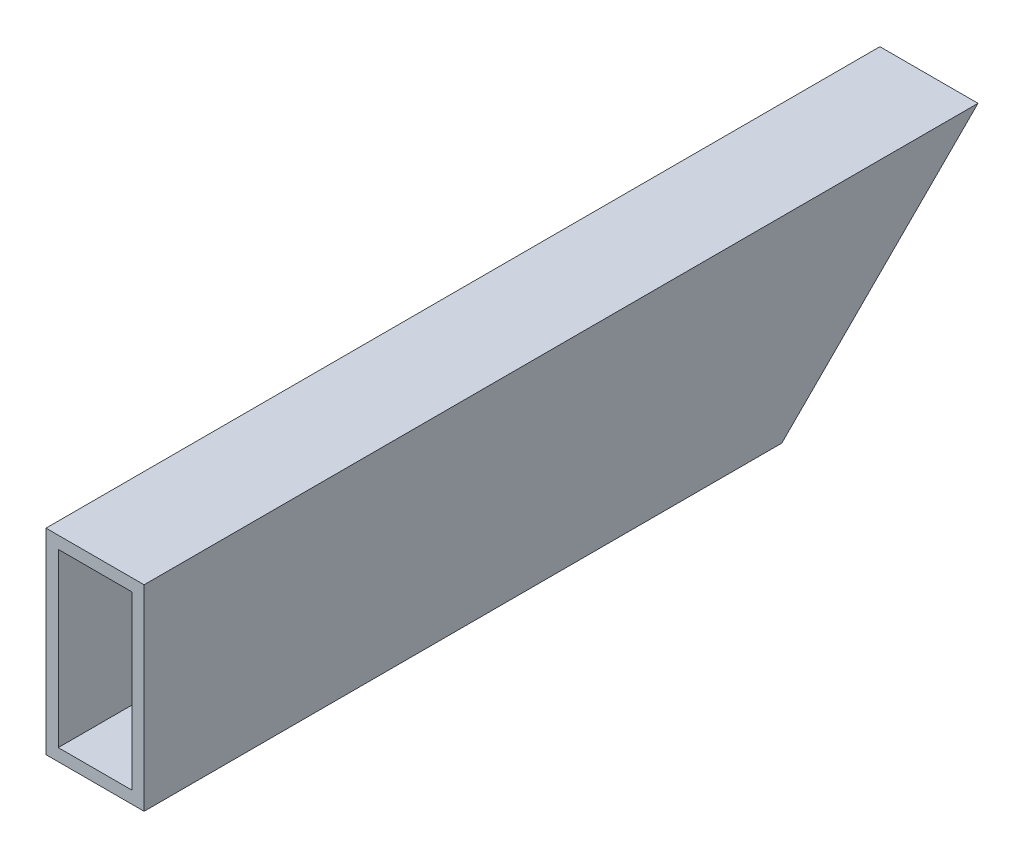
SolidWorks part; units mm, degrees
ref_plane "Front Plane" through (0, 0, 0) normal (0, 0, 1) x (1, 0, 0)
ref_plane "Top Plane" through (0, 0, 0) normal (0, 1, 0) x (1, 0, 0)
ref_plane "Right Plane" through (0, 0, 0) normal (1, 0, 0) x (0, 0, -1)
sketch "Sketch1" plane through (0, 0, 0) normal (0, 0, 1) x (1, 0, 0)
  line L2 (-22.225, 47.625) -> (-3.175, 47.625)
  line L3 (-22.225, 47.625) -> (-22.225, 3.175)
  line L4 (-22.225, 3.175) -> (-3.175, 3.175)
  line L5 (-3.175, 47.625) -> (-3.175, 3.175)
  line L6 (-25.4, 50.8) -> (0, 50.8)
  line L7 (-25.4, 50.8) -> (-25.4, 0)
  line L8 (-25.4, 0) -> (0, 0)
  line L9 (0, 50.8) -> (0, 0)
  dimension "D1" = 25.4
  dimension "D2" = 50.8
  dimension "D3" = 3.175
  dimension "D4" = 3.175
  dimension "D5" = 3.175
  dimension "D6" = 3.175
extrude "Boss-Extrude1" add sketch "Sketch1" along normal blind 215.9
sketch "Sketch2" plane through (0, 0, 0) normal (1, 0, 0) x (0, 0, -1)
  line L0 (0, 50.8) -> (-50.8, 0)
  line L1 (-215.9, 0) -> (0, 0) construction
  line L2 (-50.8, 0) -> (0, 0)
  line L3 (0, 0) -> (0, 50.8)
  line L4 (-215.9, 0) -> (-215.9, 50.8) construction
  dimension "D1" = 165.1
extrude "Cut-Extrude1" cut sketch "Sketch2" against normal blind 25.4
